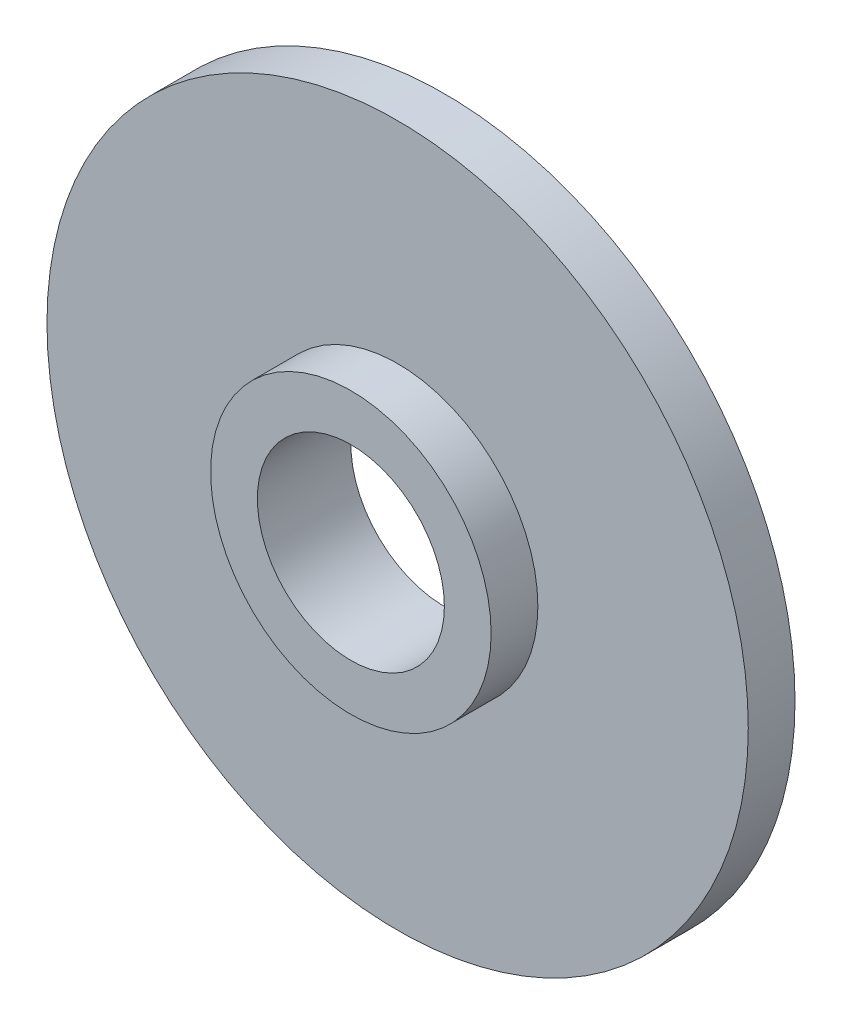
SolidWorks part; units mm, degrees
ref_plane "Front Plane" through (0, 0, 0) normal (0, 0, 1) x (1, 0, 0)
ref_plane "Top Plane" through (0, 0, 0) normal (0, 1, 0) x (1, 0, 0)
ref_plane "Right Plane" through (0, 0, 0) normal (1, 0, 0) x (0, 0, -1)
sketch "Sketch1" plane through (0, 0, 0) normal (0, 0, 1) x (1, 0, 0)
  circle A0 centre (0, 0) radius 7.5
  circle A1 centre (0, 0) radius 2
  dimension "D1" = 15
  dimension "D2" = 4
extrude "Extrude1" add sketch "Sketch1" along normal blind 1
sketch "Sketch2" plane through (0, 0, 1) normal (0, 0, 1) x (1, 0, 0)
  circle A0 centre (0, 0) radius 2
  circle A1 centre (0, 0) radius 3
  dimension "D1" = 1
extrude "Extrude2" add sketch "Sketch2" along normal blind 1
